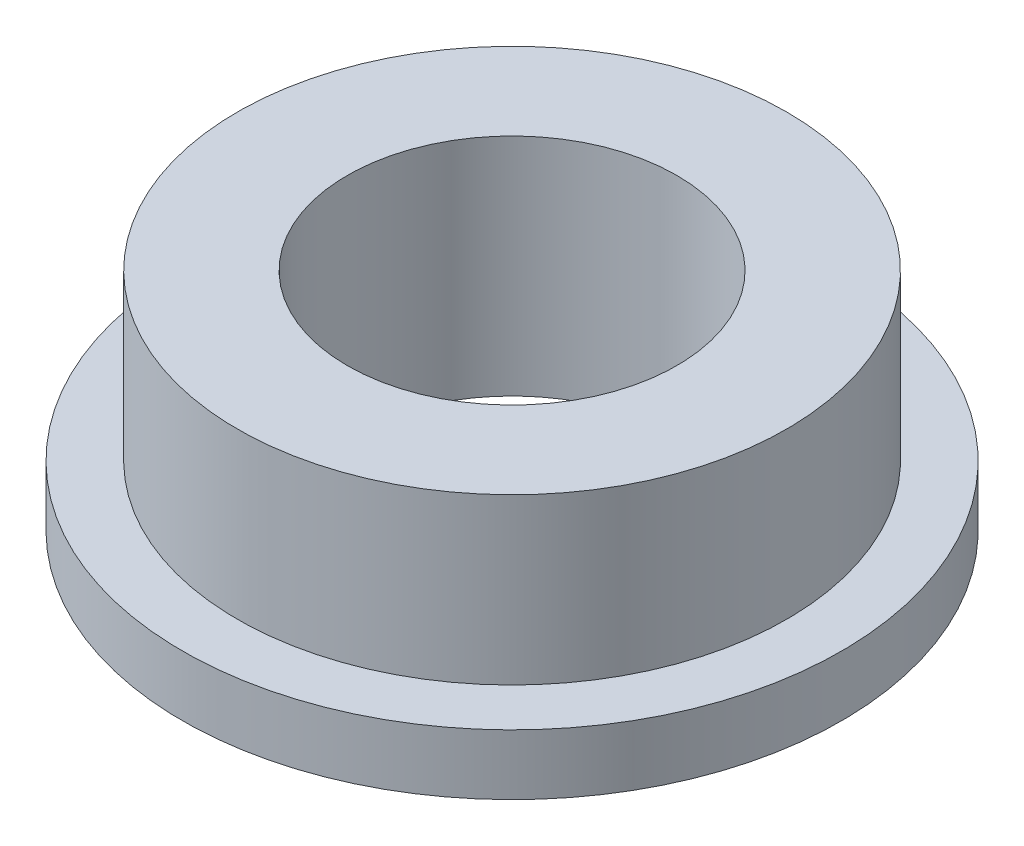
SolidWorks part; units mm, degrees
ref_plane "Front Plane" through (0, 0, 0) normal (0, 0, 1) x (1, 0, 0)
ref_plane "Top Plane" through (0, 0, 0) normal (0, 1, 0) x (1, 0, 0)
ref_plane "Right Plane" through (0, 0, 0) normal (1, 0, 0) x (0, 0, -1)
sketch "Sketch1" plane through (0, 0, 0) normal (0, 0, 1) x (1, 0, 0)
  line L0 (0, 0) -> (0, 6.2518) construction
  line L1 (-6, 0) -> (-3, 0)
  line L2 (-3, 0) -> (-3, 4.1)
  line L3 (-3, 4.1) -> (-5, 4.1)
  line L4 (-5, 4.1) -> (-5, 1.1)
  line L5 (-5, 1.1) -> (-6, 1.1)
  line L6 (-6, 1.1) -> (-6, 0)
  dimension "D1" = 1.1
  dimension "D2" = 6
  dimension "D3" = 5
  dimension "D4" = 3
  dimension "D5" = 4.1
revolve "Revolve1" add sketch "Sketch1" angle 360 about L0
